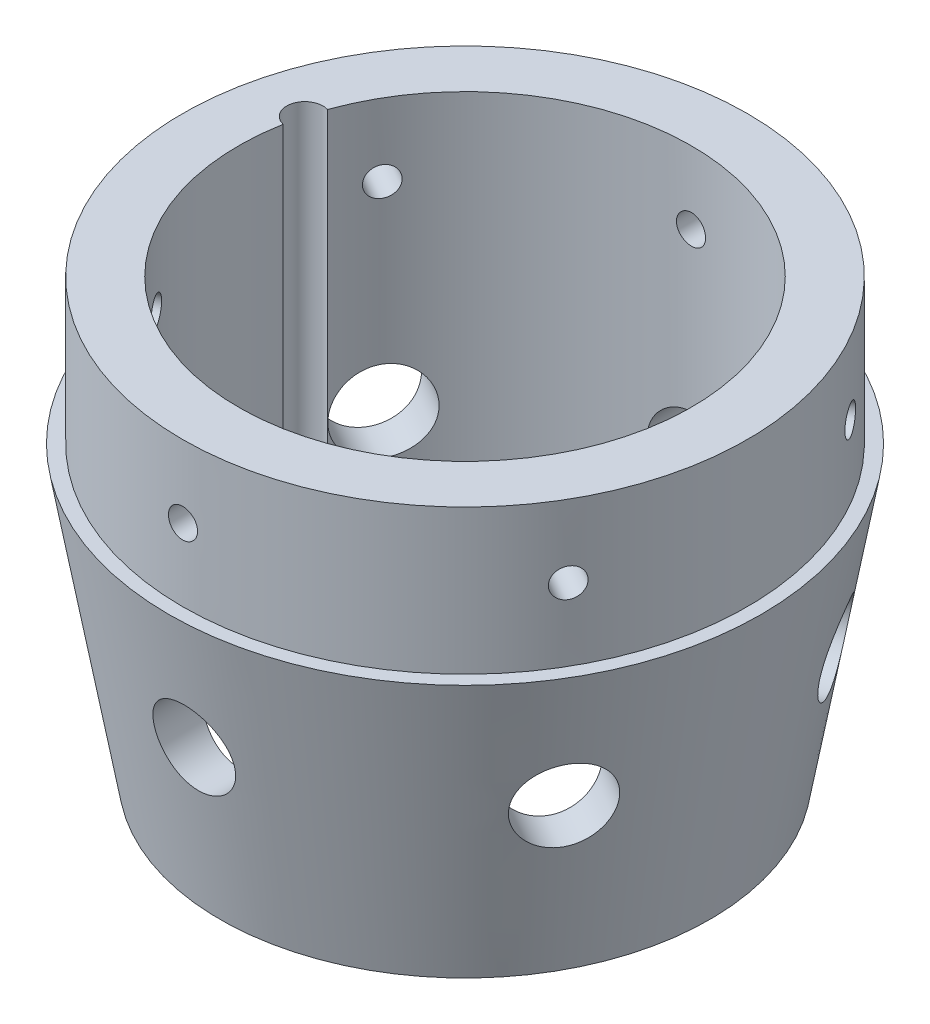
SolidWorks part; units mm, degrees
material "6061-T6 (SS)"
ref_plane "Front Plane" through (0, 0, 0) normal (0, 0, 1) x (1, 0, 0)
ref_plane "Top Plane" through (0, 0, 0) normal (0, 1, 0) x (1, 0, 0)
ref_plane "Right Plane" through (0, 0, 0) normal (1, 0, 0) x (0, 0, -1)
sketch "Sketch1" plane through (0, 0, 0) normal (0, 0, 1) x (1, 0, 0)
  line L2 (-51.9176, 50.8) -> (-49.53, 50.8)
  line L3 (-49.53, 50.8) -> (-49.53, 76.2)
  line L4 (-49.53, 76.2) -> (-39.7256, 76.2)
  line L5 (-39.7256, 76.2) -> (-39.7256, 0)
  line L6 (-39.7256, 0) -> (0, 0) construction
  line L7 (0, 0) -> (0, 68.3515) construction
  line L8 (-39.7256, 0) -> (-42.9602, 0)
  line L9 (-42.9602, 0) -> (-51.9176, 50.8)
  dimension "D1" = 49.53
  dimension "D2" = 51.9176
  dimension "D3" = 39.7256
  dimension "D4" = 10
  dimension "D5" = 25.4
  dimension "D6" = 50.8
revolve "Revolve1" add sketch "Sketch1" angle 360 about L7
ref_plane "Plane1" through (0, 0, 49.53) normal (0, 0, 1) x (1, 0, 0)
hole_wizard "Tap Drill for 1/4-20 Tap1" positions "Sketch4" profile "Sketch5" hole size "1/4-20" standard "ANSI Inch"
sketch "Sketch4" plane through (0, 0, 49.53) normal (0, 0, 1) x (1, 0, 0)
  line L3 (0, 76.2) -> (0, 50.8) construction
  line L4 (39.7256, 76.2) -> (-39.7256, 76.2) construction
  line L5 (51.9176, 50.8) -> (-51.9176, 50.8) construction
  point P9 (0, 63.5)
  point P26 (0, 63.5)
sketch "Sketch5" plane through (0, 63.5, 49.53) normal (1, 0, 0) x (0, -1, 0)
  line L0 (0, 0) -> (0, 9.8044)
  line L1 (0, 9.8044) -> (2.5527, 9.8044)
  line L2 (2.5527, 9.8044) -> (2.5527, 0)
  line L5 (2.5527, 0) -> (0, 0)
  line L11 (0, -6.35) -> (0, 107.95) construction
  dimension "Thru Hole Dia." = 5.1054
  dimension "Thru Hole Depth" = 9.8044
pattern_circular "CirPattern1" count 6 over 360 about axis through (0, 0, 0) along (0, -1, 0) of "Tap Drill for 1/4-20 Tap1"
sketch "Sketch6" plane through (0, 0, 0) normal (1, 0, 0) x (0, 0, -1)
  line L0 (0, 0) -> (42.9602, 0) construction
  line L1 (42.9602, 0) -> (49.1184, 34.925) construction
  line L3 (42.9602, 0) -> (51.9176, 50.8) construction
  point P7 (49.1184, 34.925)
  dimension "D1" = 34.925
ref_plane "Plane2" through (0, 0, -49.1184) normal (0, 0, 1) x (1, 0, 0)
sketch "Sketch12" plane through (0, 76.2, 0) normal (0, 1, 0) x (1, 0, 0)
  line L0 (0, 0) -> (-38.372, 10.2817) construction
  line L1 (-38.372, 10.2817) -> (-38.372, 0) construction
  line L2 (-38.372, 0) -> (0, 0) construction
  circle A0 centre (-38.372, 10.2817) radius 3.175
  circle A6 centre (0, 0) radius 39.7256 construction
  dimension "D1" = 6.35
  dimension "D2" = 15
extrude "Cut-Extrude2" cut sketch "Sketch12" against normal through all
ref_plane "Plane4" through (0, 0, -76.2) normal (0, 0, 1) x (1, 0, 0)
hole_wizard "9/16 (0.5625) Diameter Hole7" positions "Sketch20" profile "Sketch21" hole size "9/16" standard "ANSI Inch"
sketch "Sketch20" plane through (0, 0, -76.2) normal (0, 0, 1) x (1, 0, 0)
  point P0 (0, 28.6126)
  dimension "D1" = 28.6126
sketch "Sketch21" plane through (0, 28.6126, -76.2) normal (1, 0, 0) x (0, 1, 0)
  line L0 (0, 0) -> (0, 36.4744)
  line L1 (0, 36.4744) -> (7.1437, 36.4744)
  line L2 (7.1437, 36.4744) -> (7.1437, 0)
  line L5 (7.1437, 0) -> (0, 0)
  line L11 (0, -6.35) -> (0, 107.95) construction
  dimension "Thru Hole Dia." = 14.2875
  dimension "Thru Hole Depth" = 36.4744
ref_axis "Axis1" through (0, 80.01, 0) along (0, -1, 0)
pattern_circular "CirPattern2" count 6 over 360 about axis through (0, 80.01, 0) along (0, -1, 0) of "9/16 (0.5625) Diameter Hole7"
